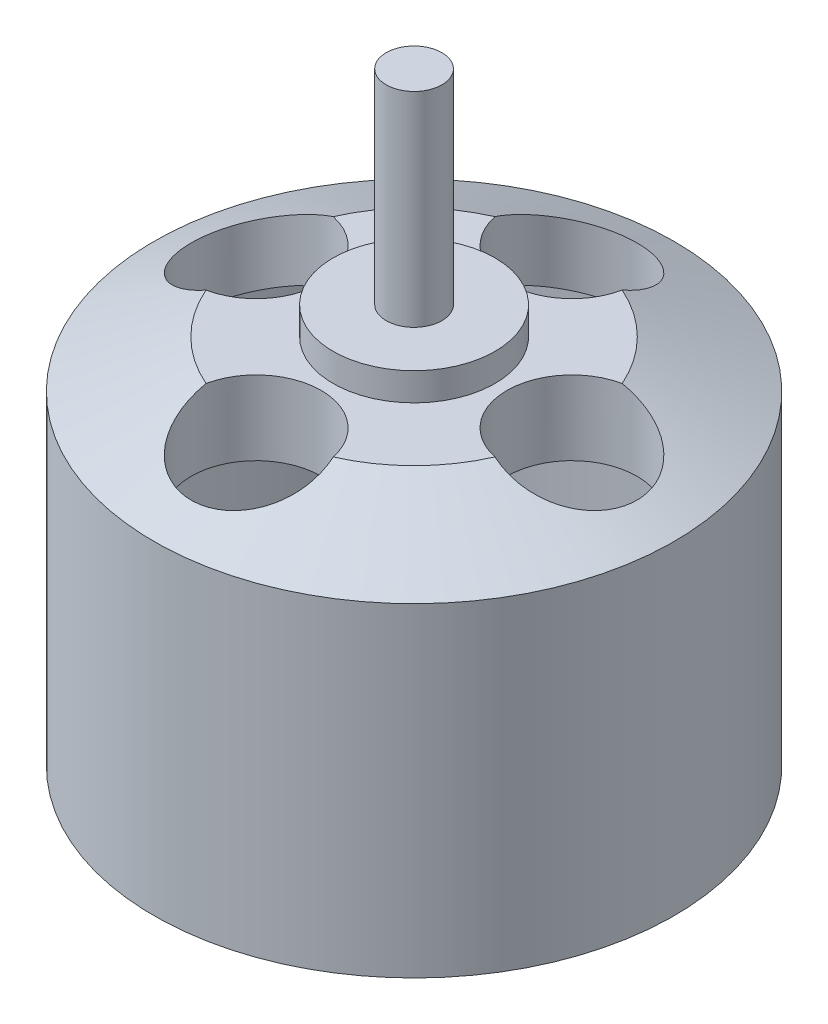
SolidWorks part; units mm, degrees
ref_plane "Alzado" through (0, 0, 0) normal (0, 0, 1) x (1, 0, 0)
ref_plane "Planta" through (0, 0, 0) normal (0, 1, 0) x (1, 0, 0)
ref_plane "Vista lateral" through (0, 0, 0) normal (1, 0, 0) x (0, 0, -1)
sketch "Croquis1" plane through (0, 0, 0) normal (0, 0, 1) x (1, 0, 0)
  line L0 (0, -19.447) -> (0, 20.1721) construction
  line L1 (-14, -16) -> (-14, 1.4537)
  line L2 (-14, 1.4537) -> (-8.5, 4)
  line L3 (-8.5, 4) -> (-4.36, 4)
  line L4 (-4.36, 4) -> (-4.36, 5.5)
  line L5 (-4.36, 5.5) -> (0, 5.5)
  line L6 (0, 5.5) -> (0, 0)
  line L7 (0, 0) -> (-10, 0)
  line L8 (-10, 0) -> (-13.24, -1.5)
  line L9 (-13.24, -1.5) -> (-13.24, -16)
  line L10 (-13.24, -16) -> (-14, -16)
  line L11 (-15.412, -16) -> (0.9168, -16) construction
  line L12 (-19.0353, 0) -> (14.901, 0) construction
  line L13 (0, 5.5) -> (0, 16.5)
  line L14 (0, 16.5) -> (-1.5, 16.5)
  line L15 (-1.5, 16.5) -> (-1.5, 5.5)
  line L16 (-1.5, 5.5) -> (0, 5.5)
  dimension "D1" = 14
  dimension "D2" = 0.76
  dimension "D3" = 20
  dimension "D4" = 4
  dimension "D5" = 14.5
  dimension "D6" = 10
  dimension "D7" = 8.5
  dimension "D8" = 4.36
  dimension "D9" = 1.5
  dimension "D10" = 11
  dimension "D11" = 1.5
revolve "Revolución1" add sketch "Croquis1" angle 360 about L0
sketch "Croquis2" plane through (0, 4, 0) normal (0, 1, 0) x (1, 0, 0)
  line L0 (-19.2643, 0) -> (21.7004, 0) construction
  line L1 (0, 16.5796) -> (0, -17.0162) construction
  circle A0 centre (0, 0) radius 8.5 construction
  circle A1 centre (0, 0) radius 8.5 construction
  circle A2 centre (0, 8.5) radius 3.5
  circle A3 centre (8.5, 0) radius 3.5
  circle A4 centre (0, -8.5) radius 3.5
  circle A5 centre (-8.5, 0) radius 3.5
  point P10 (0, 0)
  point P11 (0, 0)
  point P12 (-8.7334, 0.8378)
  point P19 (0, 0)
  point P20 (0, 0)
  dimension "D2" = 7
  dimension "D1" = 4
extrude "Cortar-Extruir1" cut sketch "Croquis2" against normal blind 7
